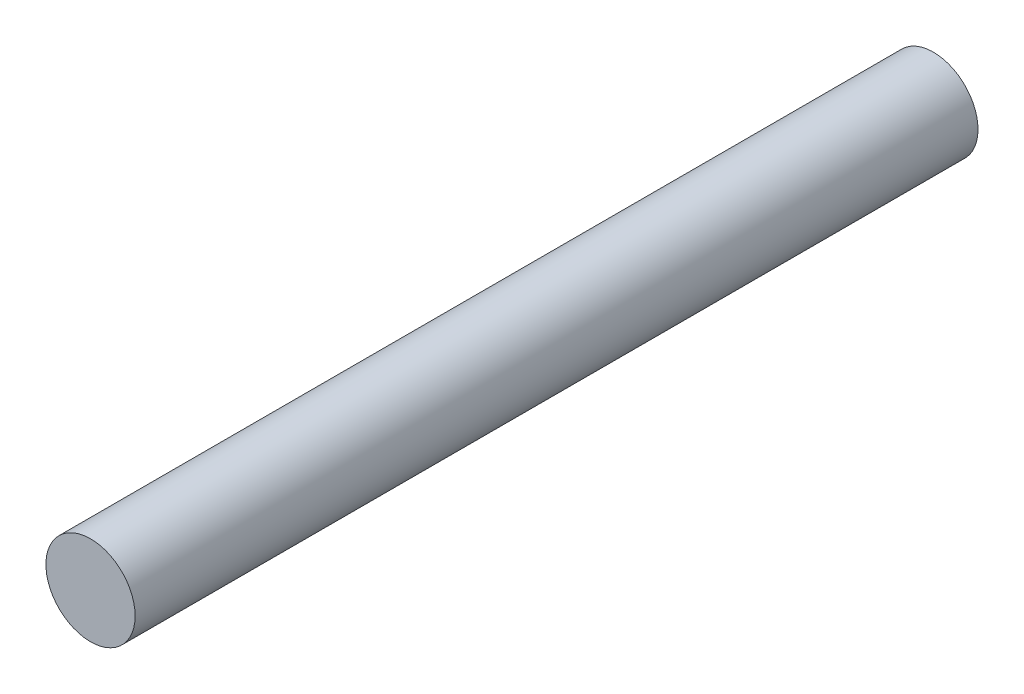
SolidWorks part; units mm, degrees
ref_plane "Front Plane" through (0, 0, 0) normal (0, 0, 1) x (1, 0, 0)
ref_plane "Top Plane" through (0, 0, 0) normal (0, 1, 0) x (1, 0, 0)
ref_plane "Right Plane" through (0, 0, 0) normal (1, 0, 0) x (0, 0, -1)
sketch "Sketch1" plane through (0, 0, 0) normal (0, 0, 1) x (1, 0, 0)
  circle A0 centre (0, 0) radius 24.875
  dimension "D1" = 49.75
extrude "Boss-Extrude1" add sketch "Sketch1" along normal blind 470.02
